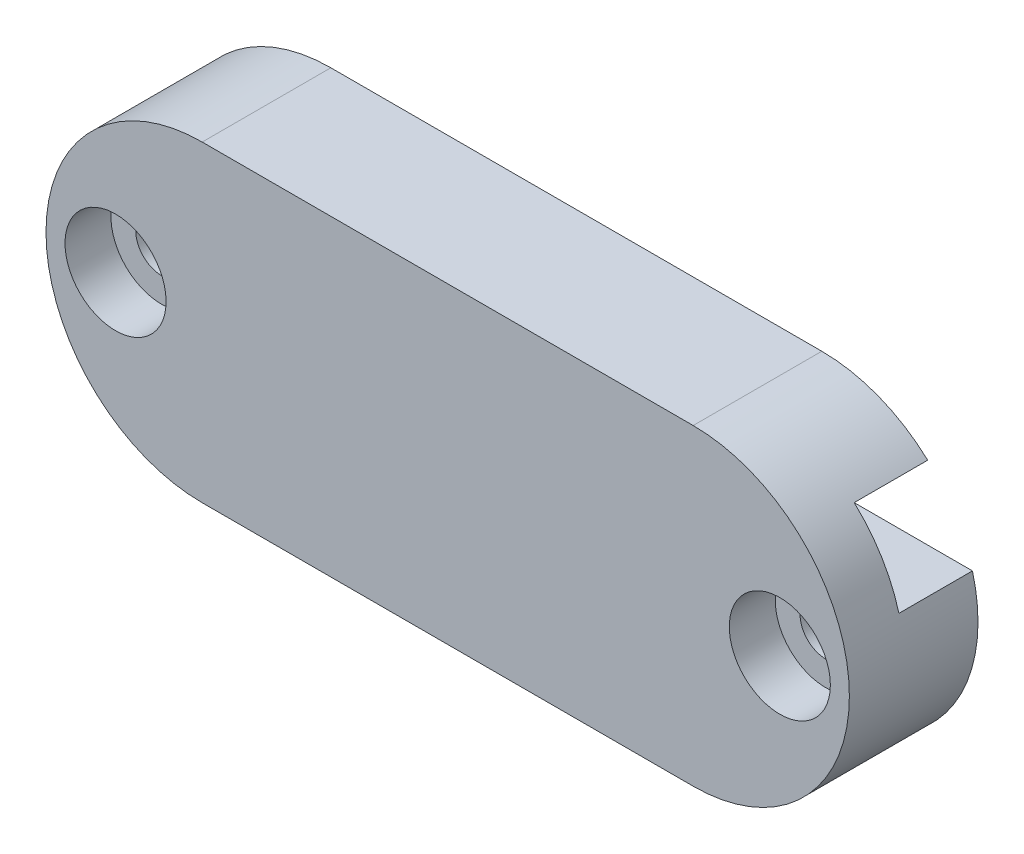
SolidWorks part; units mm, degrees
ref_plane "Front Plane" through (0, 0, 0) normal (0, 0, 1) x (1, 0, 0)
ref_plane "Top Plane" through (0, 0, 0) normal (0, 1, 0) x (1, 0, 0)
ref_plane "Right Plane" through (0, 0, 0) normal (1, 0, 0) x (0, 0, -1)
sketch "Sketch1" plane through (0, 0, 0) normal (0, 0, 1) x (1, 0, 0)
  line L0 (0, -8.5) -> (0, 8.5) construction
  line L5 (-14.9, 7.4) -> (14.9, 7.4) construction
  line L6 (-13.3594, -8.5) -> (13.3594, -8.5)
  line L8 (-13.3594, 8.5) -> (13.3594, 8.5)
  arc A3 (-13.3594, 8.5) -> (-13.3594, -8.5) centre (-13.3594, 0) ccw
  arc A4 (13.3594, 8.5) -> (13.3594, -8.5) centre (13.3594, 0) cw
  point P0 (0, 0)
  dimension "D1" = 17
extrude "Boss-Extrude1" add sketch "Sketch1" along normal blind 7 contours L8 A4 L6 A3
sketch "Sketch3" plane through (16.4, 0, 0) normal (1, 0, 0) x (0, 0, -1)
  line L0 (0, 5.7409) -> (0, 2.0329) construction
  line L1 (-4, 6.2476) -> (4, 6.2476)
  line L2 (-4, 6.2476) -> (-4, 2.2476)
  line L3 (-4, 2.2476) -> (4, 2.2476)
  line L4 (4, 6.2476) -> (4, 2.2476)
  line L5 (-4, 6.2476) -> (4, 2.2476) construction
  line L6 (-4, 2.2476) -> (4, 6.2476) construction
  point P0 (0, 4.2476)
  point P6 (0, 0)
  point P8 (0, 0)
  point P9 (0, 0)
  point P10 (0, 0)
  point P11 (0, 4.2476)
  dimension "D1" = 4
  dimension "D2" = 4
extrude "Cut-Extrude1" cut sketch "Sketch3" against normal through all both and the other way through all
sketch "Sketch6" plane through (0, 0, 0) normal (0, 0, -1) x (-1, 0, 0)
  circle A0 centre (-18.075, 0) radius 1.4
  circle A1 centre (18.075, 0) radius 1.4
extrude "Cut-Extrude3" cut sketch "Sketch6" against normal through all both and the other way through all
sketch "Sketch8" plane through (0, 0, 7) normal (0, 0, 1) x (1, 0, 0)
  circle A0 centre (-18.075, 0) radius 2.75
  circle A2 centre (18.075, 0) radius 2.75
  dimension "D1" = 5.5
extrude "Cut-Extrude4" cut sketch "Sketch8" against normal blind 2.5 and the other way through all
